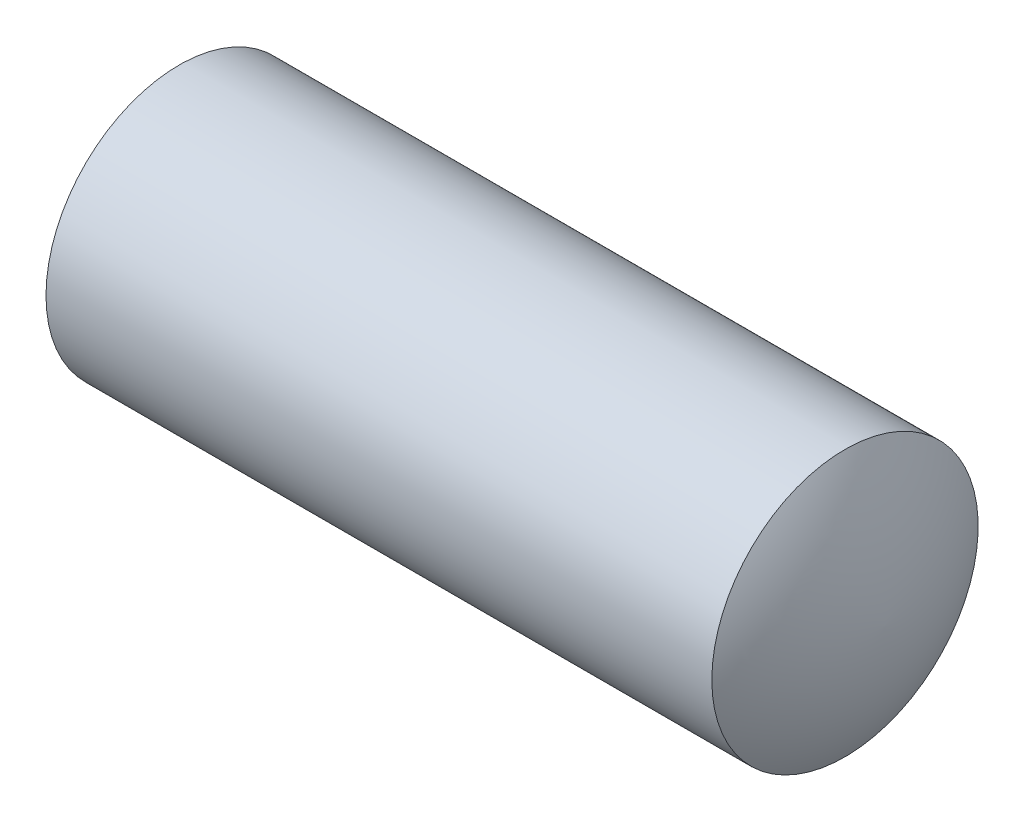
SolidWorks part; units mm, degrees
material "AISI Тип A2 Инструментальная сталь"
ref_plane "Спереди" through (0, 0, 0) normal (0, 0, 1) x (1, 0, 0)
ref_plane "Сверху" through (0, 0, 0) normal (0, 1, 0) x (1, 0, 0)
ref_plane "Справа" through (0, 0, 0) normal (1, 0, 0) x (0, 0, -1)
sketch "Эскиз1" plane through (0, 0, 0) normal (0, 0, 1) x (1, 0, 0)
  line L0 (0, 0) -> (14.3069, 0) construction
  line L1 (0, 0) -> (0, 6.3046) construction
  line L3 (0, 2) -> (10, 2)
  line L6 (10, 2) -> (10, -0.9836) construction
  line L7 (-0.6, 0) -> (10.6, 0)
  arc A1 (0, 2) -> (-0.6, 0) centre (3.3985, -0.1095) ccw
  arc A2 (10, 2) -> (10.6, 0) centre (6.6015, -0.1095) cw
  dimension "D1" = 0.6
  dimension "D4" = 4
  dimension "D6" = 4
  dimension "D2" = 4
  dimension "D3" = 10
  dimension "D5" = 0.6
revolve "Повернуть2" add sketch "Эскиз1" angle 360 about L0
